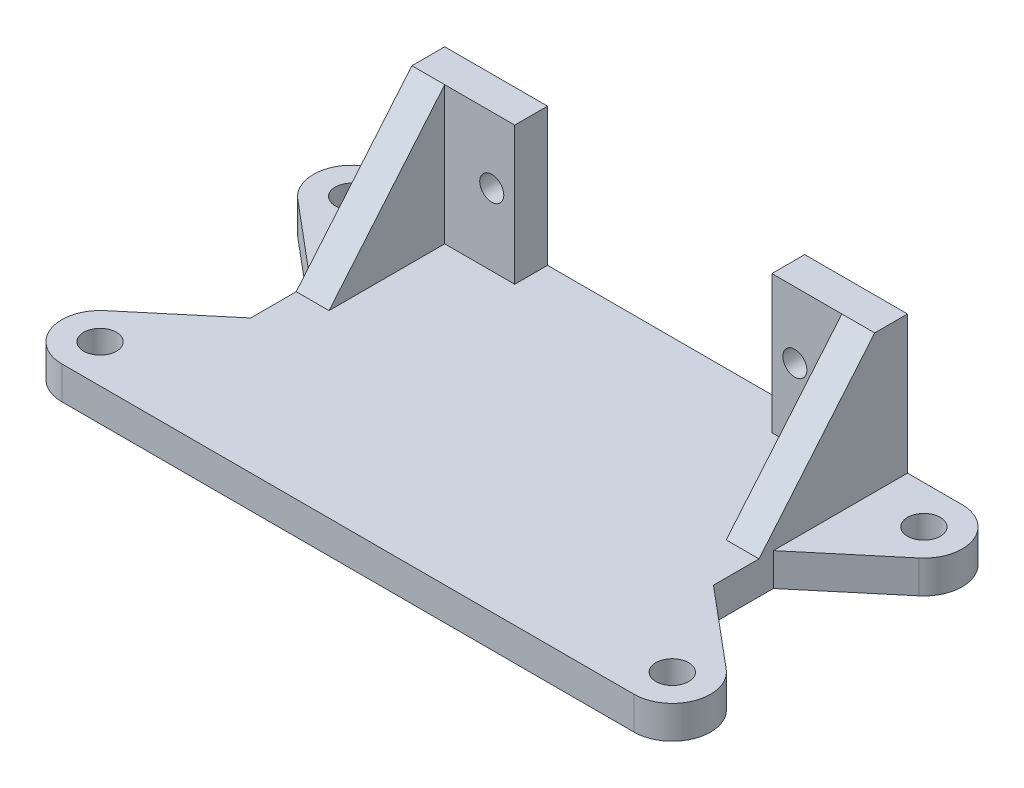
SolidWorks part; units mm, degrees
material "ABS"
ref_plane "Front Plane" through (0, 0, 0) normal (0, 0, 1) x (1, 0, 0)
ref_plane "Top Plane" through (0, 0, 0) normal (0, 1, 0) x (1, 0, 0)
ref_plane "Right Plane" through (0, 0, 0) normal (1, 0, 0) x (0, 0, -1)
sketch "Sketch2" plane through (0, 0, 0) normal (0, 0, 1) x (1, 0, 0)
  line L0 (-11.75, 3) -> (11.75, 3)
  line L1 (-16.15, 3.5) -> (16.15, 3.5) construction
  line L2 (-16.15, 3.5) -> (-16.15, 15.6) construction
  line L3 (-16.15, 15.6) -> (16.15, 15.6) construction
  line L4 (16.15, 3.5) -> (16.15, 15.6) construction
  line L5 (-11.25, 3.5) -> (11.25, 3.5) construction
  line L6 (-11.25, 3.5) -> (-11.25, 15.6) construction
  line L7 (-11.25, 15.6) -> (11.25, 15.6) construction
  line L8 (11.25, 3.5) -> (11.25, 15.6) construction
  line L9 (11.75, 3) -> (11.75, 15.6)
  line L10 (11.75, 15.6) -> (21.15, 15.6)
  line L11 (21.15, 15.6) -> (21.15, 0)
  line L12 (21.15, 0) -> (-21.15, 0)
  line L13 (-21.15, 0) -> (-21.15, 15.6)
  line L14 (-21.15, 15.6) -> (-11.75, 15.6)
  line L15 (-11.75, 15.6) -> (-11.75, 3)
  point P10 (0, 3.5)
  point P17 (0, 3)
  dimension "D1" = 32.3
  dimension "D2" = 12.1
  dimension "D3" = 22.5
  dimension "D4" = 0.5
  dimension "D5" = 0.5
  dimension "D6" = 3
  dimension "D7" = 5
extrude "Boss-Extrude1" add sketch "Sketch2" along normal blind 3 contours L11 L12 L13 L14 L15 L0 L9 L10
sketch "Sketch3" plane through (0, 0, 0) normal (0, -1, 0) x (1, 0, 0)
  line L1 (-21.15, 0) -> (21.15, 0)
  line L2 (-21.15, 0) -> (-21.15, 30)
  line L3 (-21.15, 30) -> (21.15, 30)
  line L4 (21.15, 0) -> (21.15, 30)
  dimension "D1" = 30
extrude "Boss-Extrude2" add sketch "Sketch3" against normal up to surface (3 mm away) up to face at (0, 3, 1.5)
sketch "Sketch4" plane through (0, 0, 3) normal (0, 0, 1) x (1, 0, 0)
  line L0 (-13.85, 9.55) -> (13.85, 9.55) construction
  line L1 (-21.15, 15.6) -> (-11.75, 15.6) construction
  line L2 (-16.15, 15.6) -> (16.15, 15.6) construction
  line L3 (-16.15, 15.6) -> (-16.15, 3.5) construction
  line L4 (-16.15, 3.5) -> (16.15, 3.5) construction
  line L5 (16.15, 15.6) -> (16.15, 3.5) construction
  line L6 (16.15, 9.55) -> (13.85, 9.55) construction
  circle A0 centre (13.85, 9.55) radius 1.1
  circle A1 centre (-13.85, 9.55) radius 1.1
  point P4 (0, 9.55)
  point P12 (0, 3.5)
  dimension "D1" = 2.2
  dimension "D2" = 27.7
  dimension "D3" = 32.3
  dimension "D4" = 12.1
extrude "Cut-Extrude1" cut sketch "Sketch4" against normal through all
sketch "Sketch5" plane through (21.15, 0, 0) normal (1, 0, 0) x (0, 0, -1)
  line L0 (-3, 15.6) -> (-13.5727, 3)
  line L1 (-3, 3) -> (-30, 3) construction
  line L2 (-13.5727, 3) -> (-3, 3)
  line L3 (-3, 15.6) -> (-3, 3) construction
  line L4 (-3, 3) -> (-3, 15.6)
  dimension "D1" = 40
extrude "Boss-Extrude3" add sketch "Sketch5" against normal blind 3
ref_plane "Plane1" through (0, 0, 0) normal (1, 0, 0) x (0, 0, -1)
mirror "Mirror1" about plane through (0, 0, 0) normal (1, 0, 0) of "Boss-Extrude3"
sketch "Sketch6" plane through (0, 0, 0) normal (0, -1, 0) x (1, 0, 0)
  line L0 (-21.15, 30) -> (-26.15, 30)
  line L1 (-28.3998, 23.8188) -> (-21.15, 17.7356)
  line L2 (-21.15, 30) -> (-21.15, 0) construction
  line L3 (-21.15, 30) -> (-21.15, 17.7356)
  arc A0 (-26.15, 30) -> (-28.3998, 23.8188) centre (-26.15, 26.5) ccw
  circle A1 centre (-26.15, 26.5) radius 1.5
  dimension "D1" = 3
  dimension "D2" = 2
  dimension "D3" = 5
  dimension "D4" = 50
extrude "Boss-Extrude4" add sketch "Sketch6" against normal up to surface (18.8039 mm away)
ref_plane "Plane2" through (0, 0, 15) normal (0, 0, 1) x (1, 0, 0)
mirror "Mirror2" about plane through (0, 0, 15) normal (0, 0, 1) of "Boss-Extrude4"
mirror "Mirror3" about plane through (0, 0, 0) normal (1, 0, 0) of "Mirror2", "Boss-Extrude4"
